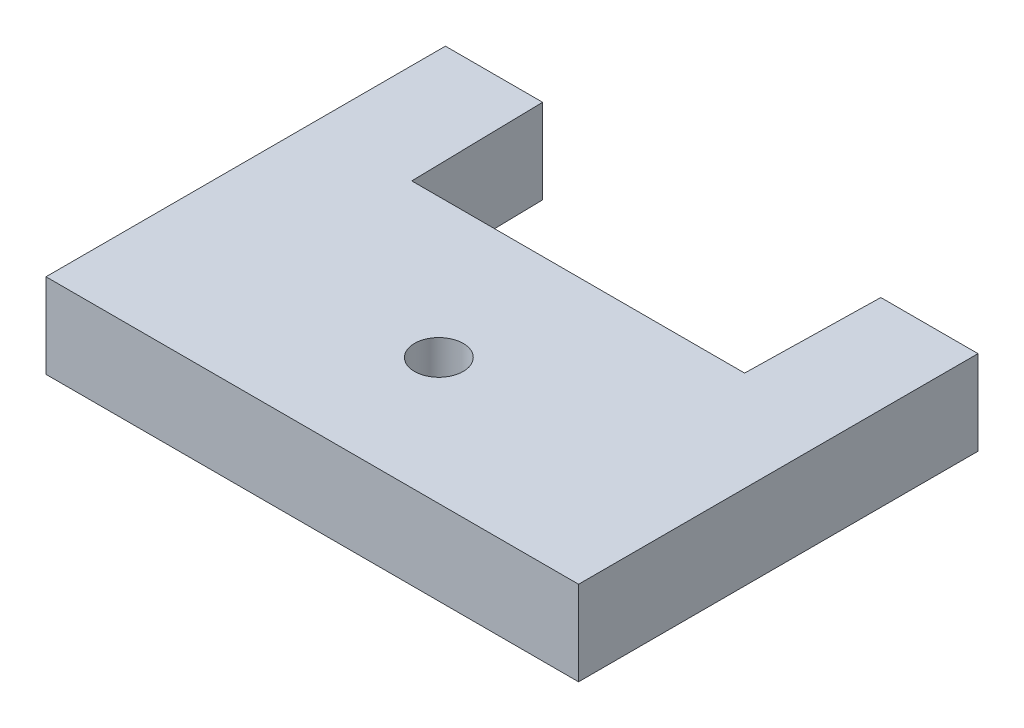
SolidWorks part; units mm, degrees
ref_plane "Front Plane" through (0, 0, 0) normal (0, 0, 1) x (1, 0, 0)
ref_plane "Top Plane" through (0, 0, 0) normal (0, 1, 0) x (1, 0, 0)
ref_plane "Right Plane" through (0, 0, 0) normal (1, 0, 0) x (0, 0, -1)
sketch "Sketch1" plane through (0, 0, 0) normal (0, 1, 0) x (1, 0, 0)
  line L1 (-20, -15) -> (20, -15)
  line L2 (-20, -15) -> (-20, 15)
  line L3 (-20, 15) -> (20, 15)
  line L4 (20, -15) -> (20, 15)
  line L5 (-20, -15) -> (20, 15) construction
  line L6 (-20, 15) -> (20, -15) construction
  point P0 (0, 0)
  dimension "D1" = 40
  dimension "D2" = 30
extrude "Boss-Extrude1" add sketch "Sketch1" along normal blind 6.35
sketch "Sketch2" plane through (0, 6.35, 0) normal (0, 1, 0) x (1, 0, 0)
  line L0 (-12.7, 15) -> (-12.5, 4.97)
  line L1 (20, 15) -> (-20, 15) construction
  line L2 (-12.5, 4.97) -> (12.5, 4.97)
  line L3 (12.5, 4.97) -> (12.7, 15)
  line L4 (12.7, 15) -> (-12.7, 15)
  point P4 (0, 4.97)
  point P8 (0, 15)
  dimension "D1" = 25.4
  dimension "D2" = 25
  dimension "D3" = 10.03
extrude "Cut-Extrude1" cut sketch "Sketch2" against normal through all
sketch "Sketch3" plane through (0, 6.35, 0) normal (0, 1, 0) x (1, 0, 0)
  line L0 (-12.5, 4.97) -> (12.5, 4.97) construction
  point P0 (0, -5.4948)
  dimension "D1" = 10.4648
hole_wizard "#6 Clearance Hole1" positions "3DSketch1" profile "Sketch4" hole size "#6" standard "ANSI Inch" end condition through all
sketch3d "3DSketch1"
  point P0 (0, 6.35, 5.4948)
sketch "Sketch4" plane through (0, 6.35, 5.4948) normal (1, 0, 0) x (0, 0, 1)
  line L0 (0, 0) -> (0, 6.35)
  line L1 (0, 6.35) -> (1.8288, 6.35)
  line L2 (1.8288, 6.35) -> (1.8288, 0)
  line L5 (1.8288, 0) -> (0, 0)
  line L11 (0, -6.35) -> (0, 107.95) construction
  dimension "Thru Hole Dia." = 3.6576
  dimension "Thru Hole Depth" = 6.35
